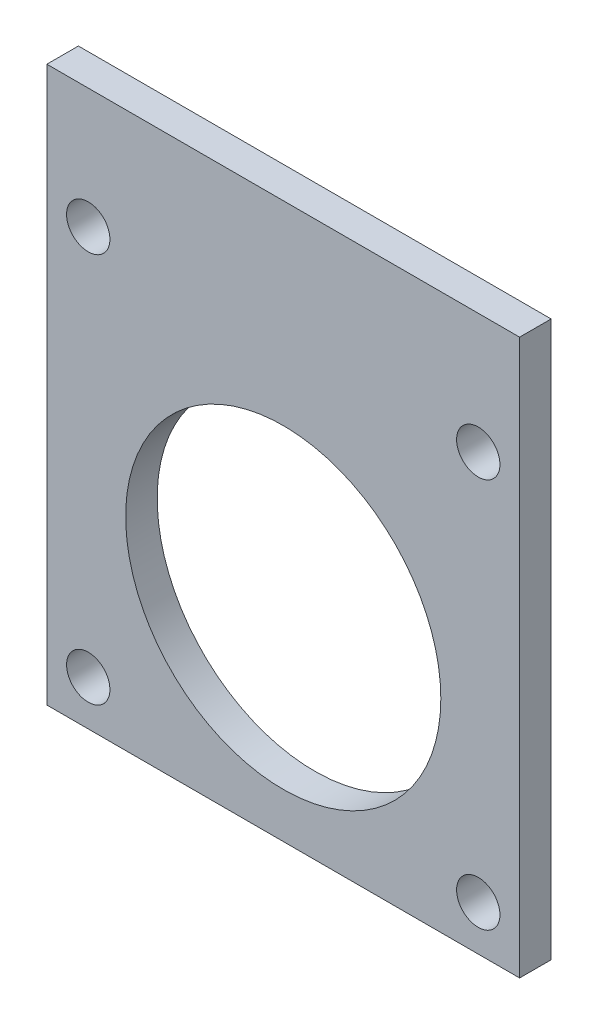
SolidWorks part; units mm, degrees
ref_plane "前基準面" through (0, 0, 0) normal (0, 0, 1) x (1, 0, 0)
ref_plane "上基準面" through (0, 0, 0) normal (0, 1, 0) x (1, 0, 0)
ref_plane "右基準面" through (0, 0, 0) normal (1, 0, 0) x (0, 0, -1)
sketch "草圖1" plane through (0, 0, 0) normal (0, 0, 1) x (1, 0, 0)
  line L1 (0, 0) -> (60, 0)
  line L2 (0, 0) -> (0, -60.44)
  line L3 (0, -60.44) -> (60, -60.44)
  line L4 (60, 0) -> (60, -60.44)
  circle A0 centre (5.25, -5.25) radius 2.75
  circle A1 centre (54.75, -5.25) radius 2.75
  circle A2 centre (5.25, -54.75) radius 2.75
  circle A3 centre (54.75, -54.75) radius 2.75
  dimension "D3" = 5.5
  dimension "D4" = 5.5
  dimension "D5" = 5.5
  dimension "D6" = 5.5
  dimension "D1" = 60
  dimension "D2" = 60.44
  dimension "D7" = 49.5
  dimension "D8" = 49.5
  dimension "D9" = 49.5
  dimension "D10" = 49.5
  dimension "D11" = 5.25
extrude "填料-伸長1" add sketch "草圖1" along normal blind 4
sketch "草圖3" plane through (0, 0, 4) normal (0, 0, 1) x (1, 0, 0)
  line L0 (60, -60.44) -> (60, 0) construction
  circle A0 centre (30, -34.7162) radius 20
  dimension "D2" = 40
  dimension "D1" = 30
extrude "除料-伸長1" cut sketch "草圖3" against normal through all
sketch "草圖6" plane through (0, 0, 0) normal (0, 1, 0) x (1, 0, 0)
  line L1 (0, 0) -> (60, 0)
  line L2 (0, 0) -> (0, -4)
  line L3 (0, -4) -> (60, -4)
  line L4 (60, 0) -> (60, -4)
  dimension "D1" = 4
extrude "填料-伸長2" add sketch "草圖6" along normal blind 10
